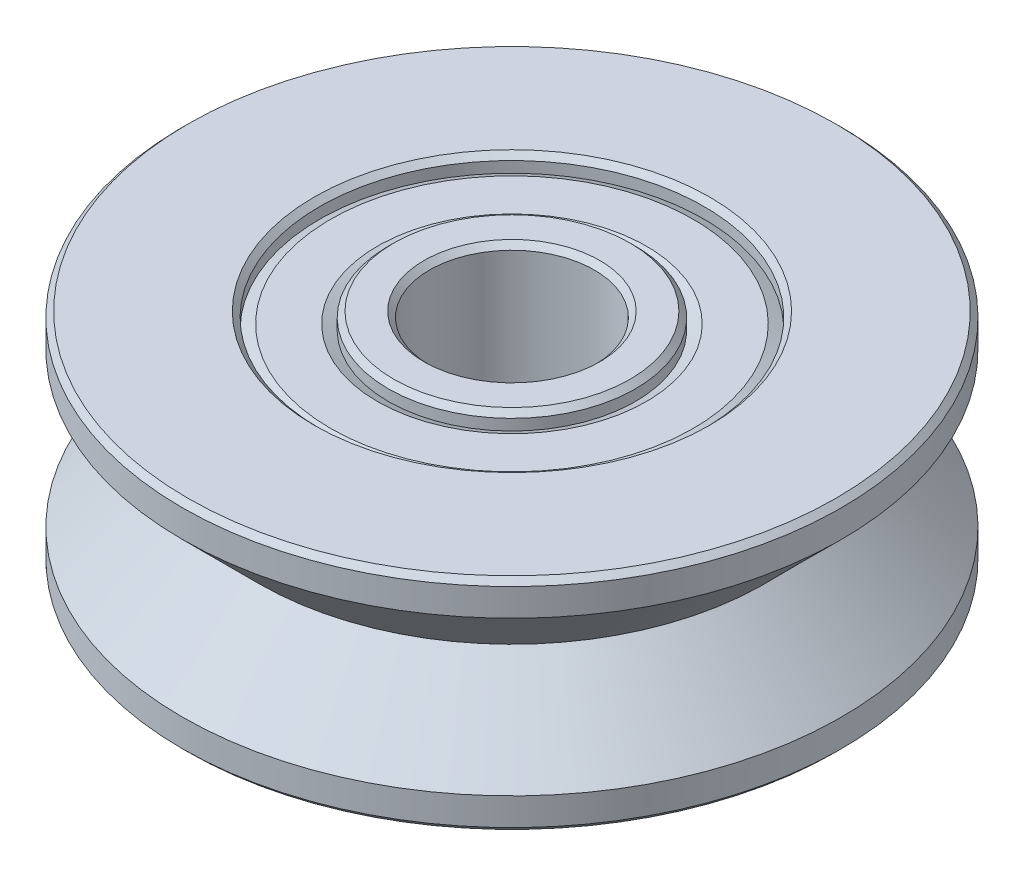
SolidWorks part; units mm, degrees
ref_plane "Front Plane" through (0, 0, 0) normal (0, 0, 1) x (1, 0, 0)
ref_plane "Top Plane" through (0, 0, 0) normal (0, 1, 0) x (1, 0, 0)
ref_plane "Right Plane" through (0, 0, 0) normal (1, 0, 0) x (0, 0, -1)
sketch "Sketch1" plane through (0, 0, 0) normal (1, 0, 0) x (0, 0, -1)
  line L0 (6, 1.4) -> (4.6, 0)
  line L1 (0, 2) -> (6, 2)
  line L2 (0, 2) -> (0, -2) construction
  line L3 (0, -2) -> (6, -2)
  line L4 (6, 2) -> (6, -2)
  line L5 (4.6, 0) -> (6, -1.4)
  line L6 (4.6, 0) -> (0, 0) construction
  line L7 (1.5, 2) -> (1.5, -2)
  dimension "D1" = 4
  dimension "D2" = 6
  dimension "D3" = 1.4
  dimension "D4" = 2.8
  dimension "D5" = 3
revolve "Revolve1" add sketch "Sketch1" angle 360 about L2
sketch "Sketch3" plane through (0, 0, 0) normal (1, 0, 0) x (0, 0, -1)
  line L0 (6, 2) -> (6, -2) construction
  line L1 (1.5, 2) -> (1.5, -2) construction
  line L2 (0, 2) -> (6, 2) construction
  line L3 (6, 2) -> (6, -2) construction
  line L4 (1.5, 2) -> (1.5, -2)
  line L5 (0, 2) -> (6, 2) construction
  line L6 (2.25, 2) -> (3.5, 2)
  line L7 (2.25, 2) -> (2.25, 1.7)
  line L8 (2.25, 1.7) -> (2.45, 1.8)
  line L9 (2.45, 1.8) -> (3.3, 1.8)
  line L10 (3.3, 1.8) -> (3.5, 1.7)
  line L11 (3.5, 1.7) -> (3.5, 2)
  line L12 (4.6, 0) -> (6, -1.4) construction
  line L13 (6, 1.4) -> (4.6, 0) construction
  line L14 (0, 2) -> (0, -2) construction
  line L15 (4.6, 0) -> (6, -1.4)
  line L16 (6, 1.4) -> (4.6, 0) construction
  line L17 (0, 2) -> (0, -2) construction
  line L18 (2.25, 1.7) -> (3.5, 1.7) construction
  line L19 (2.875, 1.7) -> (2.875, 2) construction
  dimension "D1" = 2.5
  dimension "D2" = 0.2
  dimension "D3" = 0.75
  dimension "D4" = 0.1
  dimension "D5" = 0.2
revolve "Cut-Revolve2" cut sketch "Sketch3" angle 360 about L17
mirror "Mirror1" about plane through (0, 0, 0) normal (0, 1, 0) of "Cut-Revolve2"
chamfer "Chamfer1" distance 0.1 angle 45 8 edges at (0, -2, 3.5) (0, 2, 3.5) (0, -2, 6) (0, 2, 6) (0, -2, 2.25) (0, 2, 2.25) (0, 2, 1.5) (0, -2, 1.5)
